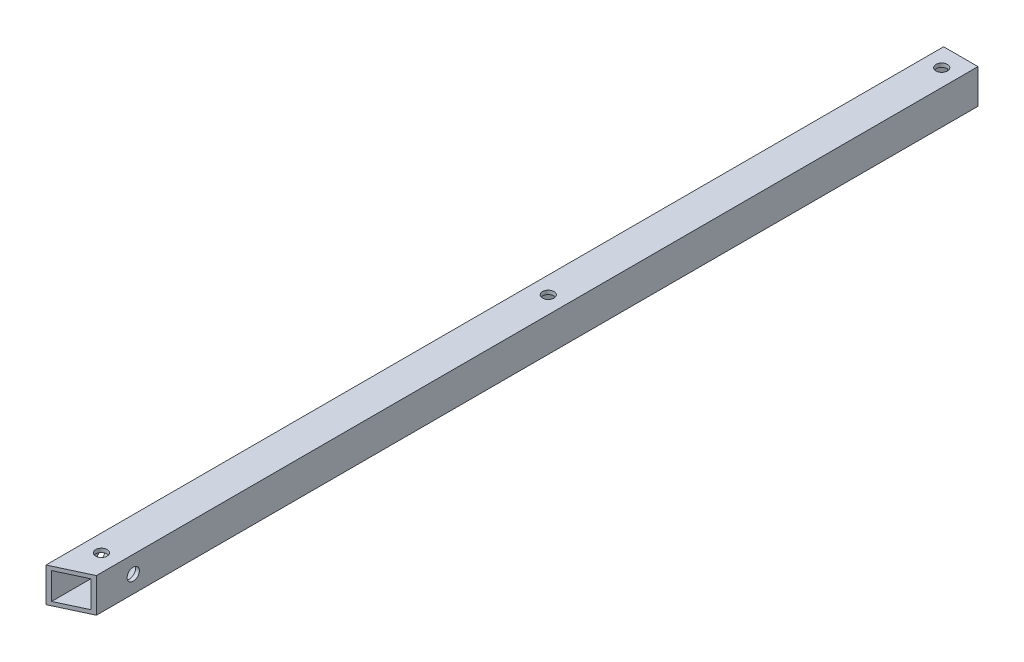
SolidWorks part; units mm, degrees
ref_plane "正面" through (0, 0, 0) normal (0, 0, 1) x (1, 0, 0)
ref_plane "平面" through (0, 0, 0) normal (0, 1, 0) x (1, 0, 0)
ref_plane "右側面" through (0, 0, 0) normal (1, 0, 0) x (0, 0, -1)
sketch "ｽｹｯﾁ1" plane through (0, 0, 0) normal (0, 0, 1) x (1, 0, 0)
  line L1 (-4.5, 4.5) -> (4.5, 4.5)
  line L2 (-4.5, 4.5) -> (-4.5, -4.5)
  line L3 (-4.5, -4.5) -> (4.5, -4.5)
  line L4 (4.5, 4.5) -> (4.5, -4.5)
  line L5 (-4.5, 4.5) -> (4.5, -4.5) construction
  line L6 (-4.5, -4.5) -> (4.5, 4.5) construction
  point P0 (0, 0)
  dimension "D1" = 9
  dimension "D2" = 9
extrude "ﾎﾞｽ - 押し出し1" add sketch "ｽｹｯﾁ1" along normal blind 235
sketch "ｽｹｯﾁ2" plane through (0, 0, 235) normal (0, 0, 1) x (1, 0, 0)
  line L1 (-3.5, 3.5) -> (3.5, 3.5)
  line L2 (-3.5, 3.5) -> (-3.5, -3.5)
  line L3 (-3.5, -3.5) -> (3.5, -3.5)
  line L4 (3.5, 3.5) -> (3.5, -3.5)
  line L5 (-3.5, 3.5) -> (3.5, -3.5) construction
  line L6 (-3.5, -3.5) -> (3.5, 3.5) construction
  point P0 (0, 0)
  dimension "D1" = 7
  dimension "D2" = 7
extrude "ｶｯﾄ - 押し出し1" cut sketch "ｽｹｯﾁ2" against normal blind 235
sketch "ｽｹｯﾁ3" plane through (0, 4.5, 0) normal (0, 1, 0) x (1, 0, 0)
  line L0 (0, 0) -> (0, -5)
  line L1 (4.5, 0) -> (-4.5, 0) construction
  line L2 (0, -5) -> (0, -108)
  line L3 (0, -108) -> (0, -225)
  circle A0 centre (0, -5) radius 1.5
  circle A1 centre (0, -108) radius 1.5
  circle A2 centre (0, -225) radius 1.5
  dimension "D3" = 3
  dimension "D4" = 3
  dimension "D6" = 3
  dimension "D1" = 5
  dimension "D2" = 103
  dimension "D5" = 117
extrude "ｶｯﾄ - 押し出し2" cut sketch "ｽｹｯﾁ3" against normal blind 235
sketch "ｽｹｯﾁ4" plane through (0, 4.5, 0) normal (0, 1, 0) x (1, 0, 0)
  line L0 (4.5, -235) -> (-4.5, -235)
  line L1 (-4.5, -235) -> (5.8988, -230.151)
  line L2 (5.8988, -230.151) -> (4.5, -235)
  dimension "D1" = 25
extrude "ｶｯﾄ - 押し出し3" cut sketch "ｽｹｯﾁ4" against normal blind 235
sketch "ｽｹｯﾁ5" plane through (4.5, 0, 0) normal (1, 0, 0) x (0, 0, -1)
  line L0 (-230.8032, 0) -> (-221.1532, 0)
  line L1 (-230.8032, 4.5) -> (-230.8032, -4.5) construction
  circle A0 centre (-221.1532, 0) radius 1.6
  dimension "D2" = 3.2
  dimension "D1" = 9.65
extrude "ｶｯﾄ - 押し出し4" cut sketch "ｽｹｯﾁ5" against normal blind 10
